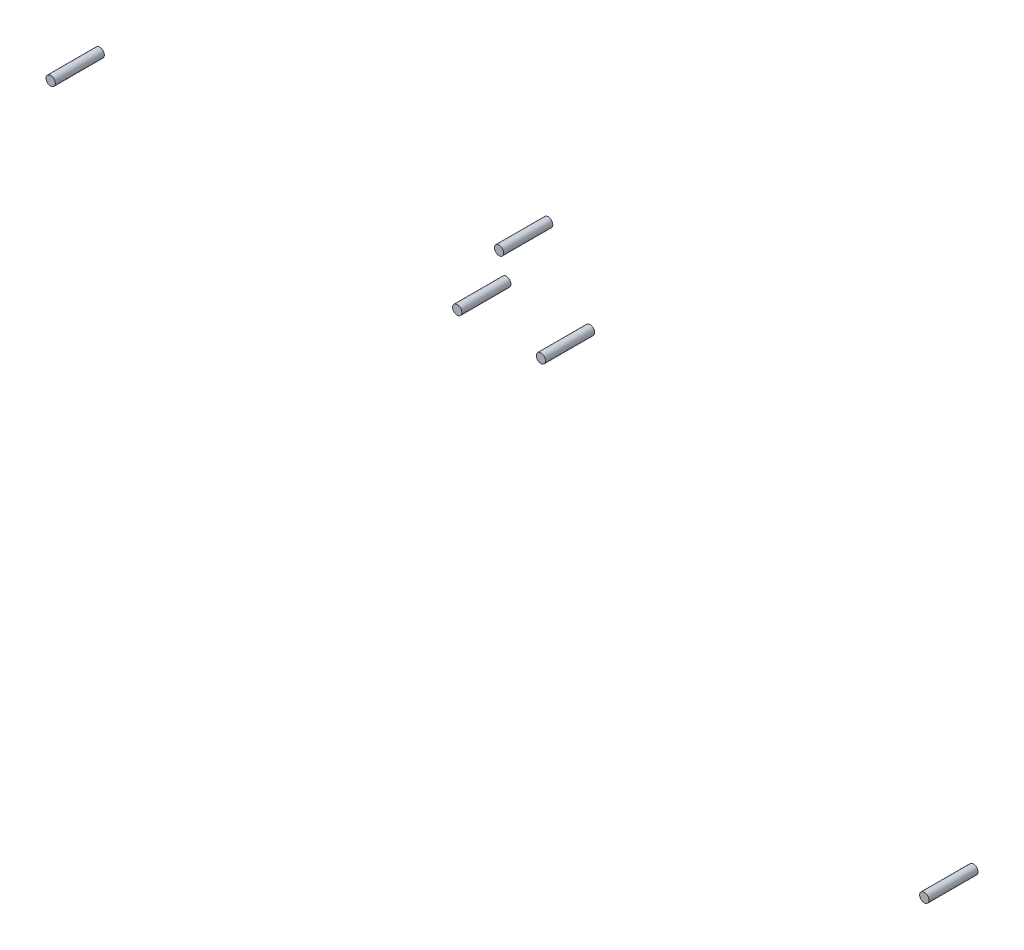
SolidWorks part; units mm, degrees
ref_plane "Front" through (0, 0, 0) normal (0, 0, 1) x (1, 0, 0)
ref_plane "Top" through (0, 0, 0) normal (0, 1, 0) x (1, 0, 0)
ref_plane "Right" through (0, 0, 0) normal (1, 0, 0) x (0, 0, -1)
sketch "Sketch2" plane through (0, 0, 0) normal (0, 0, 1) x (1, 0, 0)
  circle A0 centre (-3.0873, 50.375) radius 0.6
  circle A1 centre (-3.0873, 50.375) radius 1.1 construction
  circle A2 centre (-8.5, 59.75) radius 1.1 construction
  circle A3 centre (-13.9127, 50.375) radius 1.1 construction
  circle A4 centre (-3.0873, 50.375) radius 1.1 construction
  circle A5 centre (-8.5, 59.75) radius 1.1 construction
  circle A6 centre (-13.9127, 50.375) radius 1.1 construction
  circle A7 centre (-8.5, 59.75) radius 0.6
  circle A8 centre (-13.9127, 50.375) radius 0.6
  circle A9 centre (46.5, 14.75) radius 0.6
  circle A10 centre (-8.5, 3) radius 0.375 construction
  circle A11 centre (-8.5, 3) radius 0.375 construction
  circle A12 centre (-8.5, 72) radius 0.375 construction
  circle A13 centre (-8.5, 72) radius 0.375 construction
  circle A14 centre (-66.5, 49.75) radius 0.6
  ellipse E1 centre (-8.5, -47.8253) end of major axis (-8.875, -47.8253) minor radius 0.3689 construction
  ellipse E2 centre (-8.5, -47.8253) end of major axis (-8.875, -47.8253) minor radius 0.3689 construction
  dimension "D1" = 0.5
  dimension "D2" = 55
  dimension "D3" = 56.2411
  dimension "D4" = 79.3887
  dimension "D5" = 62.1214
  dimension "D6" = 74.4954
  dimension "D7" = 118.2962
  dimension "D8" = 45
  dimension "D9" = 58
  dimension "D10" = 10
  dimension "D11" = 83.3107
  dimension "D12" = 113.5119
  dimension "D13" = 50.8253
  dimension "D14" = 69
  dimension "D15" = 119.8253
extrude "Boss-Extrude1" add sketch "Sketch2" along normal blind 6.35
